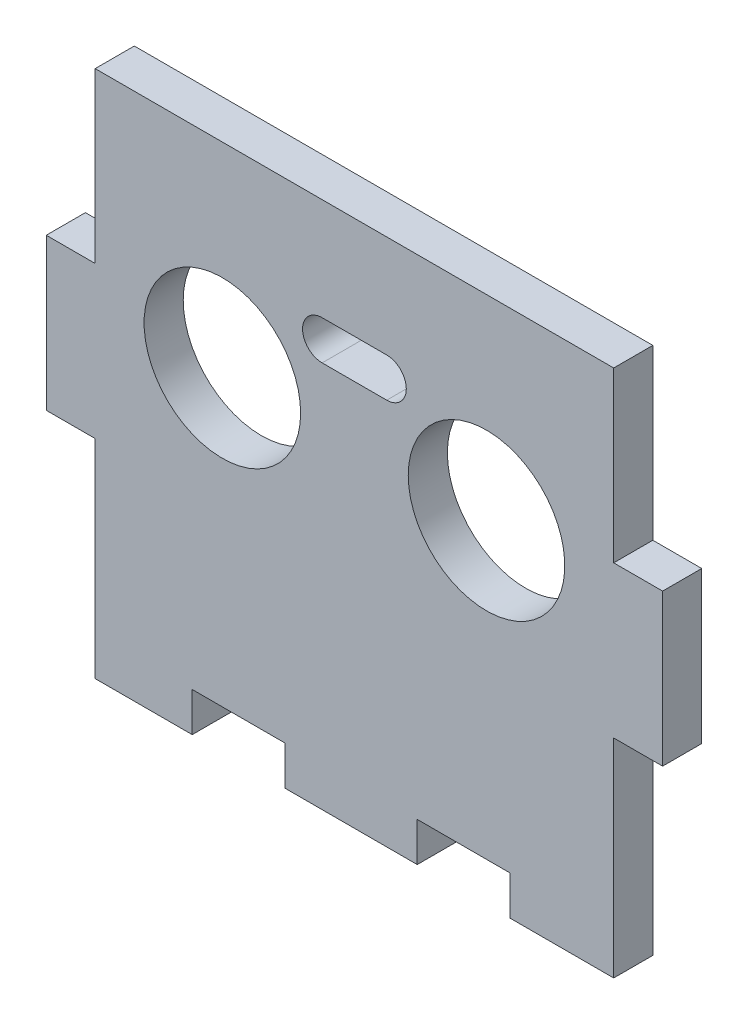
SolidWorks part; units mm, degrees
ref_plane "Ebene vorne" through (0, 0, 0) normal (0, 0, 1) x (1, 0, 0)
ref_plane "Ebene oben" through (0, 0, 0) normal (0, 1, 0) x (1, 0, 0)
ref_plane "Ebene rechts" through (0, 0, 0) normal (1, 0, 0) x (0, 0, -1)
sketch "Skizze1" plane through (0, 0, 0) normal (0, 0, 1) x (1, 0, 0)
  line L1 (0, 0) -> (63, 0)
  line L2 (0, 0) -> (0, 54)
  line L3 (0, 54) -> (63, 54)
  line L4 (63, 0) -> (63, 54)
  dimension "D1" = 54
  dimension "D2" = 63
extrude "Aufsatz-Linear austragen1" add sketch "Skizze1" along normal blind 4
sketch "Skizze4" plane through (0, 0, 4) normal (0, 0, 1) x (1, 0, 0)
  line L0 (14.9192, 0) -> (14.9192, 4)
  line L1 (0, 0) -> (63, 0) construction
  line L2 (14.9192, 4) -> (24.4192, 4)
  line L3 (24.4192, 4) -> (24.4192, 0)
  line L4 (24.4192, 0) -> (14.9192, 0)
  line L5 (37.9192, 0) -> (37.9192, 4)
  line L6 (37.9192, 4) -> (47.4192, 4)
  line L7 (47.4192, 4) -> (47.4192, 0)
  line L8 (47.4192, 0) -> (37.9192, 0)
  line L9 (31.1692, 88.1656) -> (31.1692, -34.7857) construction
  line L10 (42.6692, 14.3563) -> (42.6692, -6.7763) construction
  line L15 (37.6692, 0) -> (37.6692, 4) construction
  line L16 (24.6692, 0) -> (24.6692, 4) construction
  dimension "D1" = 4
  dimension "D2" = 9.5
  dimension "D3" = 11.5
extrude "Schnitt-Linear austragen3" cut sketch "Skizze4" against normal up to next
sketch "Skizze2" plane through (0, 0, 4) normal (0, 0, 1) x (1, 0, 0)
  line L0 (5, 54) -> (5, 36.75)
  line L1 (63, 54) -> (0, 54) construction
  line L2 (5, 36.75) -> (0, 36.75)
  line L3 (0, 54) -> (0, 0) construction
  line L5 (0, 21.25) -> (5, 21.25)
  line L6 (5, 21.25) -> (5, 0)
  line L7 (0, 0) -> (14.9192, 0) construction
  line L8 (5, 0) -> (0, 0)
  line L9 (0, 0) -> (0, 21.25)
  line L10 (0, 36.75) -> (0, 54)
  line L11 (0, 54) -> (5, 54)
  line L12 (-38.1701, 29) -> (161.0939, 29) construction
  line L13 (24.4192, 4) -> (14.9192, 4) construction
  dimension "D1" = 15.5
  dimension "D2" = 5
extrude "Schnitt-Linear austragen1" cut sketch "Skizze2" against normal up to next (4 mm away)
ref_plane "Ebene1" through (31.5, 0, 0) normal (-1, 0, 0) x (0, 0, 1)
mirror "Spiegeln1" about plane through (31.5, 0, 0) normal (-1, 0, 0) of "Schnitt-Linear austragen1"
sketch "Skizze5" plane through (0, 0, 4) normal (0, 0, 1) x (1, 0, 0)
  line L0 (-18.9865, 34) -> (89.8416, 34) construction
  line L1 (58, 54) -> (5, 54) construction
  line L2 (31.5, 2.2) -> (31.5, -2.2) construction
  line L3 (31.5, 24.4173) -> (31.5, 65.8244) construction
  line L4 (31.5, 43.55) -> (28.2, 43.55)
  line L5 (31.5, 39.55) -> (28.2, 39.55)
  line L6 (31.5, 43.55) -> (31.5, 39.55)
  circle A0 centre (18, 34) radius 8
  arc A1 (28.2, 43.55) -> (28.2, 39.55) centre (28.2, 41.55) ccw
  dimension "D2" = 16
  dimension "D4" = 2
  dimension "D1" = 20
  dimension "D3" = 13.5
extrude "Schnitt-Linear austragen4" cut sketch "Skizze5" against normal up to next (4 mm away)
mirror "Spiegeln2" about plane through (31.5, 0, 0) normal (-1, 0, 0) of "Schnitt-Linear austragen4"
